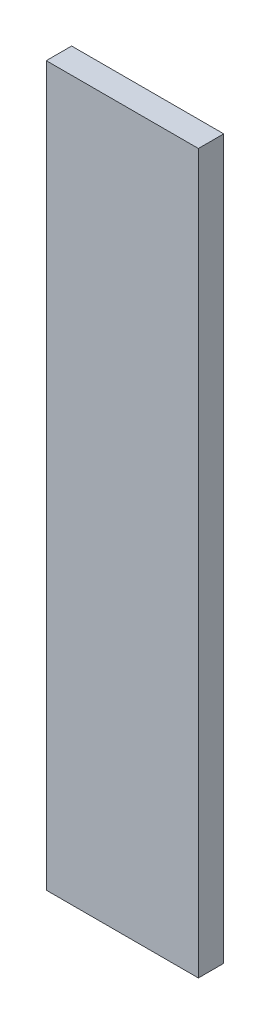
SolidWorks part; units mm, degrees
ref_plane "Plano frontal" through (0, 0, 0) normal (0, 0, 1) x (1, 0, 0)
ref_plane "Plano superior" through (0, 0, 0) normal (0, 1, 0) x (1, 0, 0)
ref_plane "Plano direito" through (0, 0, 0) normal (1, 0, 0) x (0, 0, -1)
sketch "Esboço1" plane through (0, 0, 0) normal (0, 0, 1) x (1, 0, 0)
  line L1 (-7.7344, 7.7695) -> (10.2656, 7.7695)
  line L2 (-7.7344, 7.7695) -> (-7.7344, -77.2305)
  line L3 (-7.7344, -77.2305) -> (10.2656, -77.2305)
  line L4 (10.2656, 7.7695) -> (10.2656, -77.2305)
  dimension "D1" = 18
  dimension "D2" = 85
extrude "Ressalto-extrusão1" add sketch "Esboço1" along normal blind 3
